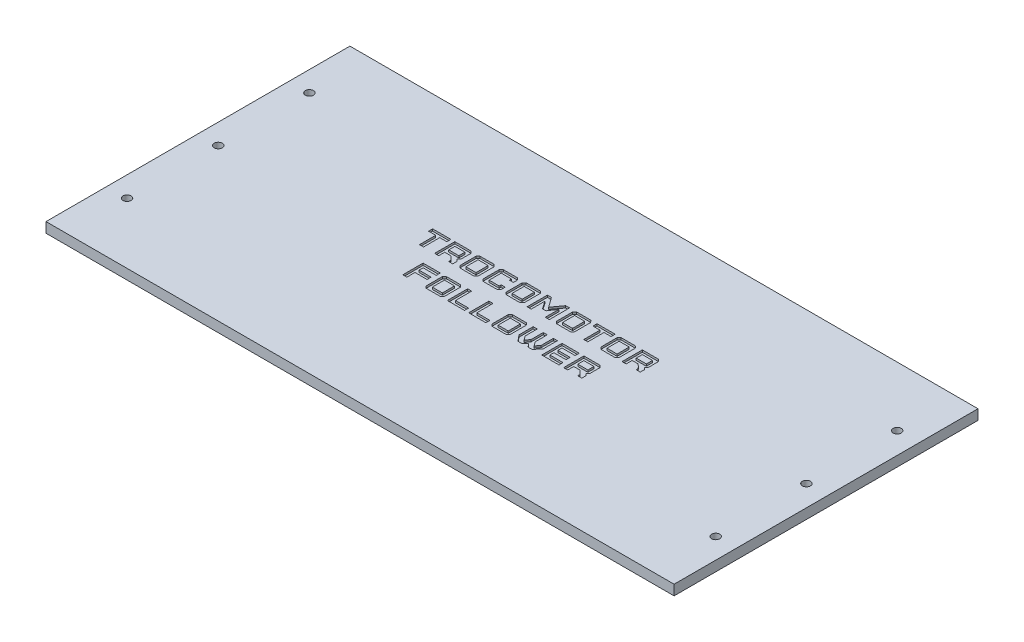
SolidWorks part; units mm, degrees
ref_plane "Front Plane" through (0, 0, 0) normal (0, 0, 1) x (1, 0, 0)
ref_plane "Top Plane" through (0, 0, 0) normal (0, 1, 0) x (1, 0, 0)
ref_plane "Right Plane" through (0, 0, 0) normal (1, 0, 0) x (0, 0, -1)
sketch "Sketch1" plane through (0, 0, 0) normal (0, 1, 0) x (1, 0, 0)
  line L1 (-155, 75) -> (155, 75)
  line L2 (-155, 75) -> (-155, -75)
  line L3 (-155, -75) -> (155, -75)
  line L4 (155, 75) -> (155, -75)
  line L5 (-155, 75) -> (155, -75) construction
  line L6 (-155, -75) -> (155, 75) construction
  point P0 (0, 0)
  dimension "D1" = 150
  dimension "D2" = 310
extrude "Boss-Extrude1" add sketch "Sketch1" along normal blind 5
sketch "Sketch2" plane through (0, 5, 0) normal (0, 1, 0) x (1, 0, 0)
  line L0 (-155, 7.3111) -> (155, 7.3111) construction
  line L1 (155, -75) -> (155, 75) construction
  text T0 "Trocomotor\r\nFollower" font "Furore" height 10
  point P5 (0, 7.3111)
extrude "Cut-Extrude1" cut sketch "Sketch2" against normal blind 1
sketch "Sketch3" plane through (0, 5, 0) normal (0, 1, 0) x (1, 0, 0)
  line L0 (-145, 75) -> (-145, -75) construction
  line L1 (155, 75) -> (-155, 75) construction
  line L2 (-155, -75) -> (155, -75) construction
  line L3 (-0.1752, 0.3111) -> (0, -75) construction
  line L4 (-155, 75) -> (-155, -75) construction
  circle A0 centre (-145, 45) radius 2
  circle A1 centre (-145, 0) radius 2
  circle A2 centre (-145, -45) radius 2
  circle A3 centre (144.8588, -44.3257) radius 2
  circle A4 centre (144.6495, 0.6739) radius 2
  circle A5 centre (144.4401, 45.6734) radius 2
  dimension "D1" = 4
  dimension "D2" = 4
  dimension "D3" = 4
  dimension "D4" = 30
  dimension "D5" = 30
  dimension "D6" = 10
extrude "Cut-Extrude2" cut sketch "Sketch3" against normal through all
